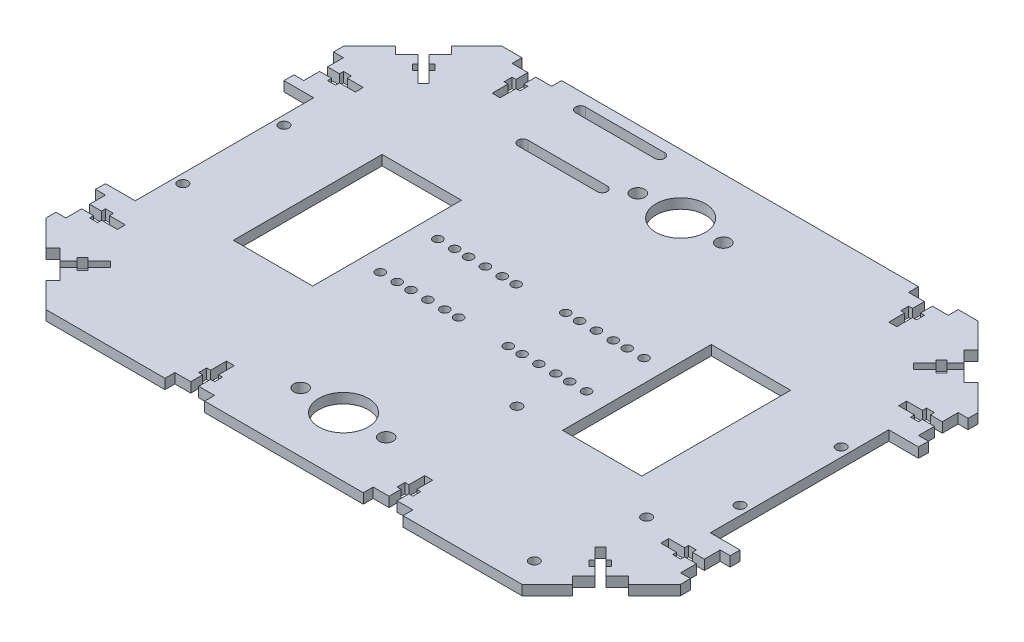
SolidWorks part; units mm, degrees
ref_plane "Front Plane" through (0, 0, 0) normal (0, 0, 1) x (1, 0, 0)
ref_plane "Top Plane" through (0, 0, 0) normal (0, 1, 0) x (1, 0, 0)
ref_plane "Right Plane" through (0, 0, 0) normal (1, 0, 0) x (0, 0, -1)
sketch "Sketch2" plane through (0, 0, 0) normal (0, 1, 0) x (1, 0, 0)
  line L1 (160, -115) -> (-160, -115)
  line L2 (160, -115) -> (160, 115)
  line L3 (160, 115) -> (-160, 115)
  line L4 (-160, -115) -> (-160, 115)
  line L5 (160, -115) -> (-160, 115) construction
  line L6 (160, 115) -> (-160, -115) construction
  point P0 (0, 0)
  dimension "D1" = 230
  dimension "D2" = 320
extrude "Boss-Extrude1" add sketch "Sketch2" along normal blind 5
sketch "Sketch5" plane through (0, 5, 0) normal (0, 1, 0) x (1, 0, 0)
  line L1 (-160, 115) -> (-160, -115) construction
  line L4 (-160, -115) -> (160, -115) construction
  line L6 (-160, 0) -> (160, 0) construction
  line L7 (160, -115) -> (160, 115) construction
  line L8 (-160, -45) -> (-160, 45)
  line L13 (0, 0) -> (0, -115) construction
  line L22 (0, 115) -> (0, 0) construction
  line L23 (160, 115) -> (-160, 115) construction
  line L24 (-55, 95) -> (60.027, 95) construction
  line L25 (-160, 45) -> (-145, 45)
  line L26 (-145, 45) -> (-145, -45)
  line L28 (-103, -37.5) -> (-103, 37.5)
  line L29 (-103, 37.5) -> (-63, 37.5)
  line L30 (-63, 37.5) -> (-63, -37.5)
  line L32 (-103, -37.5) -> (-63, -37.5)
  line L33 (-160, -45) -> (-145, -45)
  line L34 (103, -37.5) -> (63, -37.5)
  line L35 (63, 37.5) -> (63, -37.5)
  line L36 (103, 37.5) -> (63, 37.5)
  line L37 (103, -37.5) -> (103, 37.5)
  line L38 (160, 45) -> (145, 45)
  line L39 (145, 45) -> (145, -45)
  line L40 (160, -45) -> (145, -45)
  line L41 (160, -45) -> (160, 45)
  point P20 (-63, 0)
  point P21 (-103, 0)
  point P23 (-145, 0)
  dimension "D8" = 75
  dimension "D1" = 45
  dimension "D2" = 40
  dimension "D3" = 42
  dimension "D4" = 15
  dimension "D5" = 20
extrude "Cut-Extrude1" cut sketch "Sketch5" against normal through all
chamfer "Chamfer1" distance 40 distance2 40 1 edges at (-160, 2.5, -115)
chamfer "Chamfer2" distance 40 distance2 40 1 edges at (160, 2.5, -115)
chamfer "Chamfer3" distance 40 distance2 40 1 edges at (-160, 2.5, 115)
chamfer "Chamfer4" distance 40 distance2 40 1 edges at (160, 2.5, 115)
sketch "Sketch22" plane through (0, 5, 0) normal (0, 1, 0) x (1, 0, 0)
  line L0 (-145, -45) -> (-145, 45) construction
  line L1 (-145, 45) -> (-160, 45) construction
  line L2 (-160, -45) -> (-145, -45) construction
  circle A0 centre (-140.5, 25.5) radius 2.5
  circle A1 centre (-140.5, -25.5) radius 2.5
  dimension "D1" = 4.5
  dimension "D2" = 5
  dimension "D3" = 19.5
  dimension "D4" = 5
  dimension "D5" = 4.5
  dimension "D6" = 19.5
extrude "Cut-Extrude10" cut sketch "Sketch22" against normal blind 10
mirror "Mirror5" about plane through (0, 0, 0) normal (1, 0, 0) of "Cut-Extrude10"
sketch "Sketch27" plane through (0, 5, 0) normal (0, 1, 0) x (1, 0, 0)
  line L0 (-63, -37.5) -> (-63, 37.5) construction
  circle A0 centre (-52, 14.58) radius 2.25
  circle A1 centre (-52, -14.4133) radius 2.25
  circle A2 centre (-28, 14.58) radius 2.25
  circle A3 centre (-28, -14.4198) radius 2.25
  circle A4 centre (-43.5, 14.58) radius 2.25
  circle A5 centre (-36.5, 14.58) radius 2.25
  circle A6 centre (-43.5, -14.4133) radius 2.25
  circle A7 centre (-36.5, -14.4198) radius 2.25
  circle A8 centre (-19.5, 14.58) radius 2.25
  circle A9 centre (-12.5, 14.58) radius 2.25
  circle A10 centre (-19.5, -14.4198) radius 2.25
  circle A11 centre (-12.5, -14.4198) radius 2.25
  dimension "D1" = 4.5
  dimension "D2" = 4.5
  dimension "D3" = 4.5
  dimension "D4" = 4.5
  dimension "D5" = 4.5
  dimension "D6" = 4.5
  dimension "D7" = 4.5
  dimension "D8" = 4.5
  dimension "D9" = 11
  dimension "D10" = 35
  dimension "D11" = 8.5
  dimension "D12" = 7
  dimension "D13" = 11
  dimension "D14" = 35
  dimension "D15" = 8.5
  dimension "D16" = 8.5
  dimension "D17" = 7
  dimension "D18" = 24
  dimension "D19" = 4.5
  dimension "D20" = 4.5
  dimension "D21" = 24
  dimension "D22" = 24
  dimension "D23" = 8.5
  dimension "D24" = 4.5
  dimension "D25" = 4.5
  dimension "D26" = 24
  dimension "D27" = 24
  dimension "9" = 8.5
extrude "Cut-Extrude11" cut sketch "Sketch27" against normal blind 10
mirror "Mirror6" about plane through (0, 0, 0) normal (1, 0, 0) of "Cut-Extrude11"
sketch "Sketch29" plane through (0, 5, 0) normal (0, 1, 0) x (1, 0, 0)
  line L0 (0, 115) -> (0, -115) construction
  line L1 (120, 115) -> (-120, 115) construction
  line L2 (-120, -115) -> (120, -115) construction
  line L3 (0, 0) -> (-145, 0) construction
  line L4 (-145, -45) -> (-145, 45) construction
  line L5 (-160, -75) -> (-120, -115) construction
  circle A0 centre (-21.5514, -85) radius 3.5
  point P15 (-140, -95)
  dimension "D2" = 30
  dimension "D3" = 7
  dimension "D1" = 118.87
extrude "Cut-Extrude12" cut sketch "Sketch29" against normal blind 10
mirror "Mirror7" about plane through (0, 0, 0) normal (0, 0, 1) of "Cut-Extrude12" second plane through (0, 0, 0) second plane normal (1, 0, 0)
sketch "Sketch31" plane through (0, 5, 0) normal (0, 1, 0) x (1, 0, 0)
  line L0 (-32.4991, 107) -> (-72.4991, 107) construction
  line L1 (-32.4991, 104.5) -> (-72.4991, 104.5)
  line L2 (-32.4991, 109.5) -> (-72.4991, 109.5)
  line L3 (-120, 115) -> (-160, 75) construction
  line L4 (120, 115) -> (-120, 115) construction
  line L5 (-32.4991, 78) -> (-72.4991, 78) construction
  line L6 (-32.4991, 75.5) -> (-72.4991, 75.5)
  line L7 (-32.4991, 80.5) -> (-72.4991, 80.5)
  arc A0 (-32.4991, 104.5) -> (-32.4991, 109.5) centre (-32.4991, 107) ccw
  arc A1 (-72.4991, 109.5) -> (-72.4991, 104.5) centre (-72.4991, 107) ccw
  arc A2 (-32.4991, 75.5) -> (-32.4991, 80.5) centre (-32.4991, 78) ccw
  arc A3 (-72.4991, 80.5) -> (-72.4991, 75.5) centre (-72.4991, 78) ccw
  point P2 (-52.4991, 107)
  point P11 (-52.4991, 78)
  point P17 (-74.9991, 107)
  dimension "D3" = 2.5
  dimension "D1" = 8
  dimension "D2" = 40
  dimension "D4" = 29
  dimension "D5" = 2.5
  dimension "D6" = 37.4773
  dimension "D8" = 40
extrude "Cut-Extrude14" cut sketch "Sketch31" against normal blind 10
sketch "Sketch33" plane through (0, 5, 0) normal (0, 1, 0) x (1, 0, 0)
  line L0 (-120, -115) -> (120, -115) construction
  line L2 (160, -75) -> (160, -45) construction
  circle A0 centre (40.96, -38.5) radius 2.5
  circle A1 centre (122.08, -54.2) radius 2.5
  circle A2 centre (112.9, -101.65) radius 2.5
  dimension "D1" = 5
  dimension "D2" = 76.5
  dimension "D3" = 119.04
  dimension "D4" = 5
  dimension "D5" = 5
  dimension "D6" = 37.92
  dimension "D7" = 60.8
  dimension "D8" = 13.35
  dimension "D9" = 47.1
extrude "Cut-Extrude15" cut sketch "Sketch33" against normal blind 10
sketch "Sketch35" plane through (0, 5, 0) normal (0, 1, 0) x (1, 0, 0)
  line L0 (-120, -115) -> (120, -115) construction
  line L1 (40, -115) -> (60, -115)
  line L2 (40, -115) -> (40, -110)
  line L3 (40, -110) -> (60, -110)
  line L4 (60, -115) -> (60, -110)
  line L5 (160, -75) -> (160, -45) construction
  line L7 (48, -110) -> (52, -110)
  line L8 (48, -110) -> (48, -92)
  line L9 (48, -92) -> (52, -92)
  line L10 (52, -110) -> (52, -92)
  line L11 (46, -100) -> (54, -100)
  line L12 (46, -100) -> (46, -104)
  line L13 (46, -104) -> (54, -104)
  line L14 (54, -100) -> (54, -104)
  point P16 (54, -102)
  dimension "D1" = 20
  dimension "D2" = 5
  dimension "D3" = 100
  dimension "D4" = 4
  dimension "D5" = 8
  dimension "D6" = 8
  dimension "D8" = 6
  dimension "D9" = 8
  dimension "D10" = 6
  dimension "D11" = 2
  dimension "D12" = 2
  dimension "D13" = 4
  dimension "D14" = 18
extrude "Cut-Extrude16" cut sketch "Sketch35" against normal blind 10 contours L1 L4 L3 L2 | L13 L8 L3 L10 | L14 L11 L10 L13 | L8 L13 L10 L11 | L12 L13 L8 L11 | L8 L11 L10 L9
mirror "Mirror8" about plane through (0, 0, 0) normal (1, 0, 0) of "Cut-Extrude16"
sketch "Sketch36" plane through (0, 5, 0) normal (0, 1, 0) x (1, 0, 0)
  line L0 (120, 115) -> (-120, 115) construction
  line L1 (-110, 115) -> (-90, 115)
  line L2 (-110, 115) -> (-110, 110)
  line L3 (-110, 110) -> (-90, 110)
  line L4 (-90, 115) -> (-90, 110)
  line L5 (-160, 75) -> (-160, 45) construction
  line L7 (-102, 110) -> (-98, 110)
  line L8 (-102, 110) -> (-102, 92)
  line L9 (-102, 92) -> (-98, 92)
  line L10 (-98, 110) -> (-98, 92)
  line L11 (-104, 104) -> (-96, 104)
  line L12 (-104, 104) -> (-104, 100)
  line L13 (-104, 100) -> (-96, 100)
  line L14 (-96, 104) -> (-96, 100)
  dimension "D1" = 20
  dimension "D2" = 50
  dimension "D3" = 5
  dimension "D4" = 18
  dimension "D5" = 4
  dimension "D6" = 8
  dimension "D7" = 8
  dimension "D8" = 6
  dimension "D9" = 4
  dimension "D10" = 8
  dimension "D11" = 6
extrude "Cut-Extrude17" cut sketch "Sketch36" against normal blind 10 contours L4 L1 L2 L3 | L8 L11 L10 L3 | L8 L13 L10 L11 | L12 L13 L8 L11 | L14 L11 L10 L13 | L13 L8 L9 L10
mirror "Mirror9" about plane through (0, 0, 0) normal (1, 0, 0) of "Cut-Extrude17"
sketch "Sketch37" plane through (0, 5, 0) normal (0, 1, 0) x (1, 0, 0)
  line L0 (-160, -45) -> (-160, -75) construction
  line L1 (-160, -50) -> (-155, -50)
  line L2 (-160, -50) -> (-160, -70)
  line L3 (-160, -70) -> (-155, -70)
  line L4 (-155, -50) -> (-155, -70)
  line L5 (-160, -45) -> (-145, -45) construction
  line L6 (-34.6569, -53.4264) -> (-29.6569, -53.4264)
  line L7 (-155, -58) -> (-137, -58)
  line L8 (-155, -58) -> (-155, -62)
  line L9 (-155, -62) -> (-137, -62)
  line L10 (-137, -58) -> (-137, -62)
  line L11 (-149, -56) -> (-145, -56)
  line L12 (-149, -56) -> (-149, -64)
  line L13 (-149, -64) -> (-145, -64)
  line L14 (-145, -56) -> (-145, -64)
  line L15 (-34.6569, -53.4264) -> (-34.6569, -73.4264)
  line L16 (-34.6569, -73.4264) -> (-29.6569, -73.4264)
  line L17 (-29.6569, -53.4264) -> (-29.6569, -73.4264)
  line L18 (-29.6569, -61.4264) -> (-11.6569, -61.4264)
  line L19 (-29.6569, -61.4264) -> (-29.6569, -65.4264)
  line L20 (-29.6569, -65.4264) -> (-11.6569, -65.4264)
  line L21 (-11.6569, -61.4264) -> (-11.6569, -65.4264)
  line L22 (-23.6569, -59.4264) -> (-19.6569, -59.4264)
  line L23 (-23.6569, -59.4264) -> (-23.6569, -67.4264)
  line L24 (-23.6569, -67.4264) -> (-19.6569, -67.4264)
  line L25 (-19.6569, -59.4264) -> (-19.6569, -67.4264)
  line L26 (-31.1569, 10) -> (-26.1569, 10)
  line L27 (-31.1569, 10) -> (-31.1569, -10)
  line L28 (-31.1569, -10) -> (-26.1569, -10)
  line L29 (-26.1569, 10) -> (-26.1569, -10)
  line L30 (-26.1569, 2) -> (-8.1569, 2)
  line L31 (-26.1569, 2) -> (-26.1569, -2)
  line L32 (-26.1569, -2) -> (-8.1569, -2)
  line L33 (-8.1569, 2) -> (-8.1569, -2)
  line L34 (-20.1569, 4) -> (-16.1569, 4)
  line L35 (-20.1569, 4) -> (-20.1569, -4)
  line L36 (-20.1569, -4) -> (-16.1569, -4)
  line L37 (-16.1569, 4) -> (-16.1569, -4)
  line L38 (-27.6569, 10) -> (-22.6569, 10)
  line L39 (-27.6569, 10) -> (-27.6569, -10)
  line L40 (-27.6569, -10) -> (-22.6569, -10)
  line L41 (-22.6569, 10) -> (-22.6569, -10)
  line L42 (-22.6569, 2) -> (-4.6569, 2)
  line L43 (-22.6569, 2) -> (-22.6569, -2)
  line L44 (-22.6569, -2) -> (-4.6569, -2)
  line L45 (-4.6569, 2) -> (-4.6569, -2)
  line L46 (-16.6569, 4) -> (-12.6569, 4)
  line L47 (-16.6569, 4) -> (-16.6569, -4)
  line L48 (-16.6569, -4) -> (-12.6569, -4)
  line L49 (-12.6569, 4) -> (-12.6569, -4)
  line L50 (-24.1569, 10) -> (-19.1569, 10)
  line L51 (-24.1569, 10) -> (-24.1569, -10)
  line L52 (-24.1569, -10) -> (-19.1569, -10)
  line L53 (-19.1569, 10) -> (-19.1569, -10)
  line L54 (-19.1569, 2) -> (-1.1569, 2)
  line L55 (-19.1569, 2) -> (-19.1569, -2)
  line L56 (-19.1569, -2) -> (-1.1569, -2)
  line L57 (-1.1569, 2) -> (-1.1569, -2)
  line L58 (-13.1569, 4) -> (-9.1569, 4)
  line L59 (-13.1569, 4) -> (-13.1569, -4)
  line L60 (-13.1569, -4) -> (-9.1569, -4)
  line L61 (-9.1569, 4) -> (-9.1569, -4)
  line L62 (-20.6569, 10) -> (-15.6569, 10)
  line L63 (-20.6569, 10) -> (-20.6569, -10)
  line L64 (-20.6569, -10) -> (-15.6569, -10)
  line L65 (-15.6569, 10) -> (-15.6569, -10)
  line L66 (-15.6569, 2) -> (2.3431, 2)
  line L67 (-15.6569, 2) -> (-15.6569, -2)
  line L68 (-15.6569, -2) -> (2.3431, -2)
  line L69 (2.3431, 2) -> (2.3431, -2)
  line L70 (-9.6569, 4) -> (-5.6569, 4)
  line L71 (-9.6569, 4) -> (-9.6569, -4)
  line L72 (-9.6569, -4) -> (-5.6569, -4)
  line L73 (-5.6569, 4) -> (-5.6569, -4)
  line L74 (-17.1569, 10) -> (-12.1569, 10)
  line L75 (-17.1569, 10) -> (-17.1569, -10)
  line L76 (-17.1569, -10) -> (-12.1569, -10)
  line L77 (-12.1569, 10) -> (-12.1569, -10)
  line L78 (-12.1569, 2) -> (5.8431, 2)
  line L79 (-12.1569, 2) -> (-12.1569, -2)
  line L80 (-12.1569, -2) -> (5.8431, -2)
  line L81 (5.8431, 2) -> (5.8431, -2)
  line L82 (-6.1569, 4) -> (-2.1569, 4)
  line L83 (-6.1569, 4) -> (-6.1569, -4)
  line L84 (-6.1569, -4) -> (-2.1569, -4)
  line L85 (-2.1569, 4) -> (-2.1569, -4)
  line L86 (-120, -115) -> (-60, -115) construction
  point P89 (-157.5, -70)
  dimension "D1" = 20
  dimension "D2" = 5
  dimension "D3" = 5
  dimension "D4" = 5
  dimension "D5" = 18
  dimension "D6" = 4
  dimension "D7" = 8
  dimension "D8" = 8
  dimension "D9" = 13
  dimension "D10" = 6
  dimension "D11" = 4
  dimension "D12" = 8
  dimension "D13" = 6
  dimension "D14" = 6
  dimension "D15" = 45
extrude "Cut-Extrude18" cut sketch "Sketch37" against normal blind 10 contours L12 L7 L4 L9 | L14 L7 L12 L9 | L14 L11 L12 L7 | L14 L9 L12 L13 | L7 L14 L9 L10
mirror "Mirror10" about plane through (0, 0, 0) normal (0, 0, 1) of "Cut-Extrude18" second plane through (0, 0, 0) second plane normal (1, 0, 0)
sketch "Sketch39" plane through (0, 5, 0) normal (0, 1, 0) x (1, 0, 0)
  line L0 (-146.8701, -88.1299) -> (-132.7279, -102.2721)
  line L1 (-160, -75) -> (-120, -115) construction
  line L2 (-132.7279, -102.2721) -> (-129.1924, -98.7365)
  line L3 (-129.1924, -98.7365) -> (-143.3345, -84.5944)
  line L4 (-143.3345, -84.5944) -> (-146.8701, -88.1299)
  line L5 (-134.8492, -93.0797) -> (-122.1213, -80.3518)
  line L6 (-122.1213, -80.3518) -> (-124.9497, -77.5233)
  line L7 (-124.9497, -77.5233) -> (-137.6777, -90.2513)
  line L8 (-134.8492, -84.5944) -> (-129.1924, -90.2513)
  line L9 (-134.8492, -84.5944) -> (-132.0208, -81.766)
  line L10 (-132.0208, -81.766) -> (-126.364, -87.4228)
  line L11 (-126.364, -87.4228) -> (-129.1924, -90.2513)
  dimension "D1" = 5
  dimension "D2" = 20
  dimension "D3" = 18
  dimension "D4" = 18.5685
  dimension "D5" = 4
  dimension "D6" = 8
  dimension "D7" = 8
  dimension "D8" = 18
  dimension "D9" = 6
  dimension "D10" = 4
  dimension "D11" = 6
  dimension "D12" = 8
  dimension "D13" = 6
extrude "Cut-Extrude19" cut sketch "Sketch39" against normal blind 10 contours L3 L4 L0 L2 | L8 L7 L3 L5 | L10 L7 L8 L5 | L10 L9 L8 L7 | L11 L10 L5 L8 | L7 L10 L5 L6
mirror "Mirror11" about plane through (0, 0, 0) normal (1, 0, 0) of "Cut-Extrude19" second plane through (0, 0, 0) second plane normal (0, 0, 1)
sketch "Sketch40" plane through (0, 5, 0) normal (0, 1, 0) x (1, 0, 0)
  circle A1 centre (-21.5514, -85) radius 3.5 construction
  circle A4 centre (0.0514, -85) radius 12.5
  circle A6 centre (21.5514, -85) radius 3.5 construction
  dimension "D1" = 21.6027
  dimension "D2" = 25
  dimension "D3" = 21.5
extrude "Cut-Extrude20" cut sketch "Sketch40" against normal blind 10
mirror "Mirror12" about plane through (0, 0, 0) normal (0, 0, 1) of "Cut-Extrude20"
